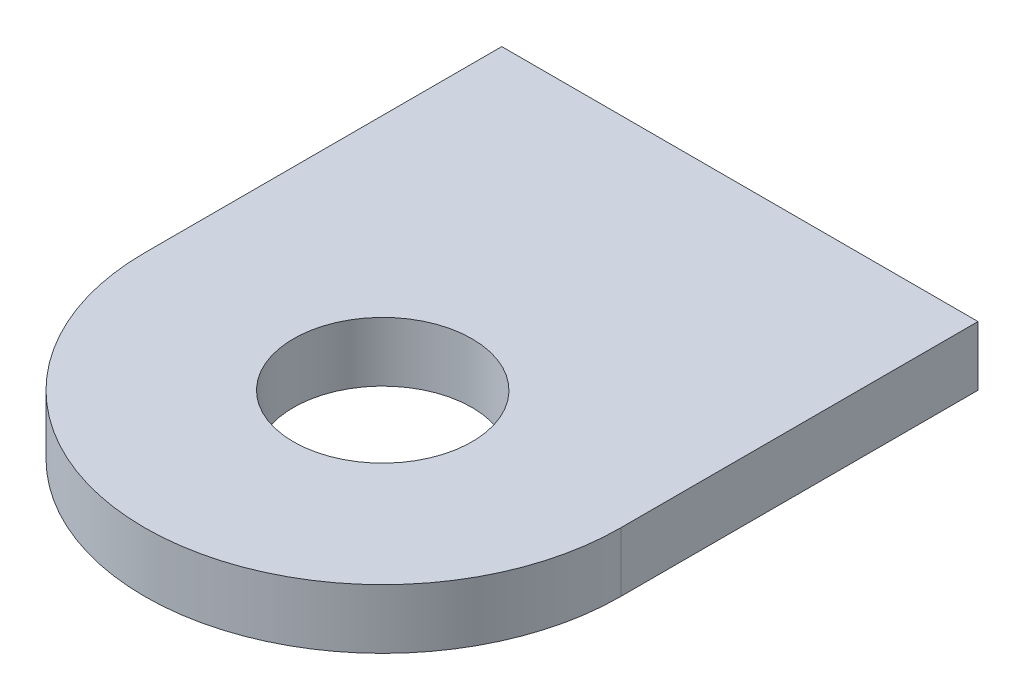
SolidWorks part; units mm, degrees
ref_plane "Front Plane" through (0, 0, 0) normal (0, 0, 1) x (1, 0, 0)
ref_plane "Top Plane" through (0, 0, 0) normal (0, 1, 0) x (1, 0, 0)
ref_plane "Right Plane" through (0, 0, 0) normal (1, 0, 0) x (0, 0, -1)
sketch "Sketch1" plane through (0, 0, 0) normal (0, 1, 0) x (1, 0, 0)
  line L0 (-25.4, 0) -> (-25.4, -38.1)
  line L1 (-55, 0) -> (55, 0) construction
  line L2 (25.4, -38.1) -> (25.4, 0)
  line L3 (25.4, 0) -> (-25.4, 0)
  line L4 (0, -55) -> (0, 55) construction
  arc A0 (-25.4, -38.1) -> (25.4, -38.1) centre (0, -38.1) ccw
  circle A1 centre (0, -38.1) radius 9.525
  dimension "D1" = 19.05
  dimension "D2" = 50.8
  dimension "D3" = 38.1
extrude "Boss-Extrude1" add sketch "Sketch1" along normal mid plane 6.35
